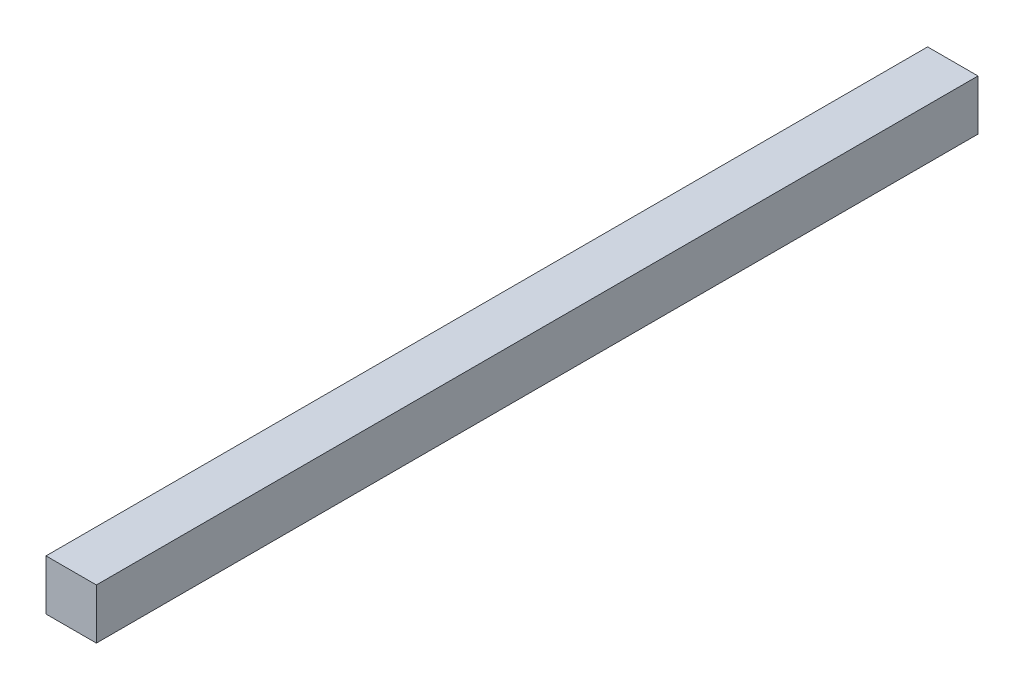
SolidWorks part; units mm, degrees
ref_plane "Płaszczyzna przednia" through (0, 0, 0) normal (0, 0, 1) x (1, 0, 0)
ref_plane "Płaszczyzna górna" through (0, 0, 0) normal (0, 1, 0) x (1, 0, 0)
ref_plane "Płaszczyzna prawa" through (0, 0, 0) normal (1, 0, 0) x (0, 0, -1)
sketch "Szkic1" plane through (0, 0, 0) normal (0, 0, 1) x (1, 0, 0)
  line L1 (0, 0) -> (20, 0)
  line L2 (0, 0) -> (0, 20)
  line L3 (0, 20) -> (20, 20)
  line L4 (20, 0) -> (20, 20)
  dimension "D1" = 20
  dimension "D2" = 20
extrude "Dodanie-wyciągnięcie1" add sketch "Szkic1" against normal blind 350
